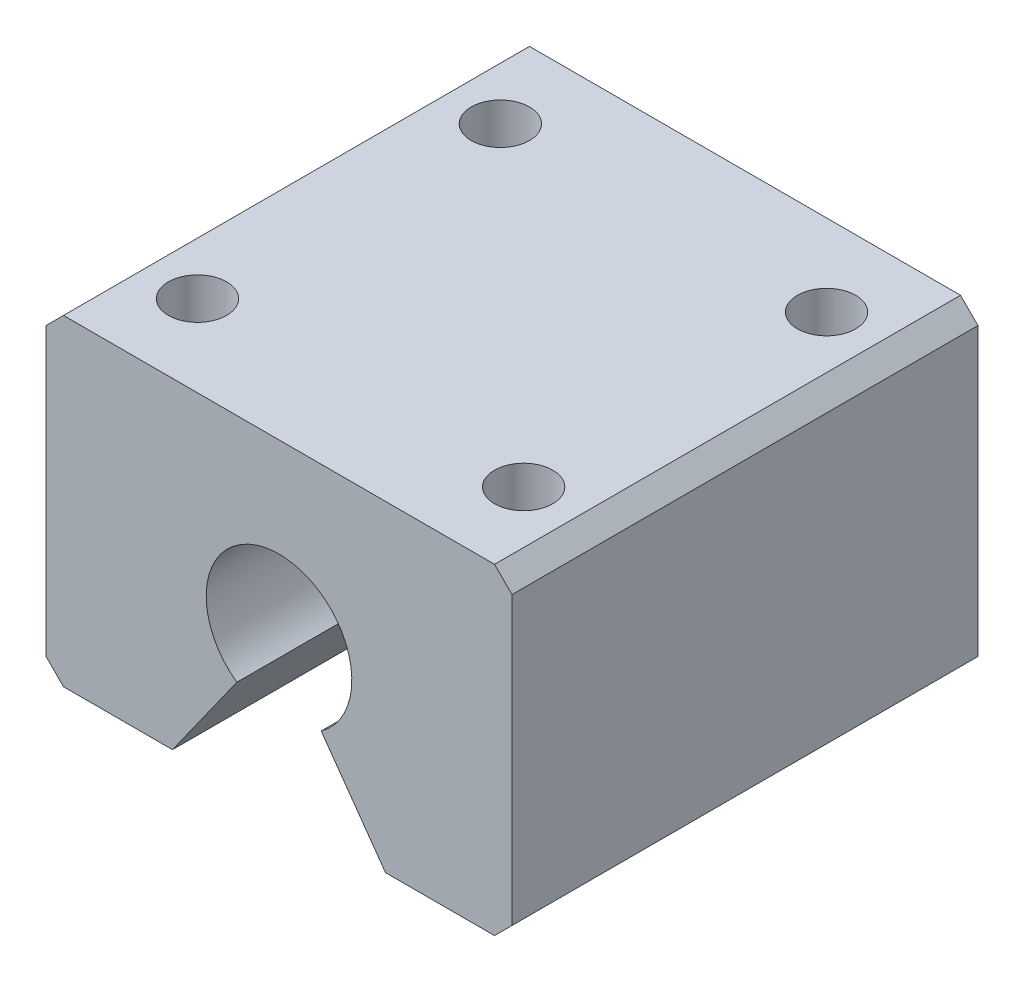
SolidWorks part; units mm, degrees
ref_plane "Front Plane" through (0, 0, 0) normal (0, 0, 1) x (1, 0, 0)
ref_plane "Top Plane" through (0, 0, 0) normal (0, 1, 0) x (1, 0, 0)
ref_plane "Right Plane" through (0, 0, 0) normal (1, 0, 0) x (0, 0, -1)
sketch "Sketch1" plane through (0, 0, 0) normal (0, 1, 0) x (1, 0, 0)
  line L1 (-20, 20) -> (20, 20)
  line L2 (-20, 20) -> (-20, -20)
  line L3 (-20, -20) -> (20, -20)
  line L4 (20, 20) -> (20, -20)
  line L5 (-20, 20) -> (20, -20) construction
  line L6 (-20, -20) -> (20, 20) construction
  point P0 (0, 0)
  dimension "D1" = 40
  dimension "D2" = 40
extrude "Boss-Extrude1" add sketch "Sketch1" along normal blind 27.6
sketch "Sketch2" plane through (0, 0, 20) normal (0, 0, 1) x (1, 0, 0)
  line L0 (9.1412, 0) -> (-9.1412, 0)
  line L1 (-20, 0) -> (20, 0) construction
  line L2 (-9.1412, 0) -> (-3.6197, 7.7721)
  line L3 (0, 24.4337) -> (0, 12.8672) construction
  line L4 (9.1412, 0) -> (3.6197, 7.7721)
  arc A0 (3.6197, 7.7721) -> (-3.6197, 7.7721) centre (0, 12.8672) ccw
  point P10 (0, 0)
  dimension "D1" = 12.5
extrude "Cut-Extrude1" cut sketch "Sketch2" against normal through all
sketch "Sketch3" plane through (0, 27.6, 0) normal (0, 1, 0) x (1, 0, 0)
  line L1 (14, -13) -> (-14, -13) construction
  line L2 (14, -13) -> (14, 13) construction
  line L3 (14, 13) -> (-14, 13) construction
  line L4 (-14, -13) -> (-14, 13) construction
  line L5 (14, -13) -> (-14, 13) construction
  line L6 (14, 13) -> (-14, -13) construction
  circle A0 centre (-14, 13) radius 2.5
  circle A1 centre (14, 13) radius 2.5
  circle A2 centre (14, -13) radius 2.5
  circle A3 centre (-14, -13) radius 2.5
  point P0 (0, 0)
  dimension "D3" = 5
  dimension "D1" = 26
  dimension "D2" = 28
extrude "Cut-Extrude2" cut sketch "Sketch3" against normal blind 14.6
chamfer "Chamfer1" distance 1.5 angle 45 4 edges at (20, 0, 0) (-20, 0, 0) (20, 27.6, 0) (-20, 27.6, 0)
